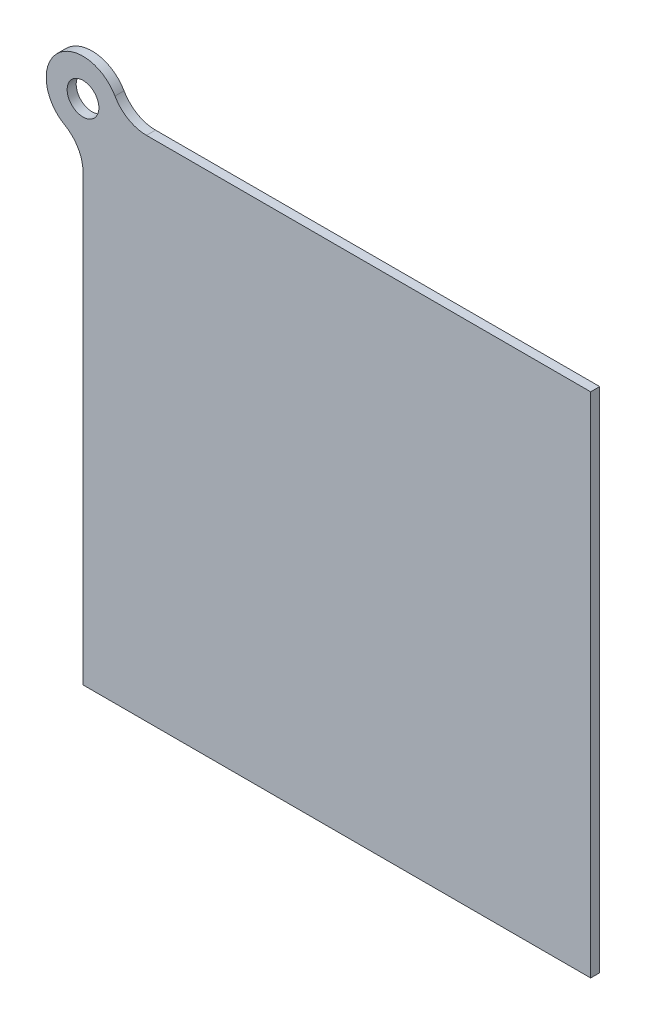
SolidWorks part; units mm, degrees
ref_plane "Front Plane" through (0, 0, 0) normal (0, 0, 1) x (1, 0, 0)
ref_plane "Top Plane" through (0, 0, 0) normal (0, 1, 0) x (1, 0, 0)
ref_plane "Right Plane" through (0, 0, 0) normal (1, 0, 0) x (0, 0, -1)
sketch "Sketch1" plane through (0, 0, 0) normal (0, 0, 1) x (1, 0, 0)
  line L0 (0, -10.3124) -> (0, -142.24)
  line L1 (0, -142.24) -> (142.24, -142.24)
  line L2 (142.24, -142.24) -> (142.24, 0)
  line L3 (142.24, 0) -> (10.3124, 0)
  circle A0 centre (0, 0) radius 4.445
  arc A1 (10.3124, 0) -> (0, -10.3124) centre (0, 0) ccw
  dimension "D1" = 8.89
  dimension "D2" = 10.3124
  dimension "D3" = 142.24
  dimension "D4" = 142.24
extrude "Boss-Extrude1" add sketch "Sketch1" along normal blind 2.54
fillet "Fillet1" radius 10.16 2 edges at (0, -10.3124, 1.27) (10.3124, 0, 1.27)
